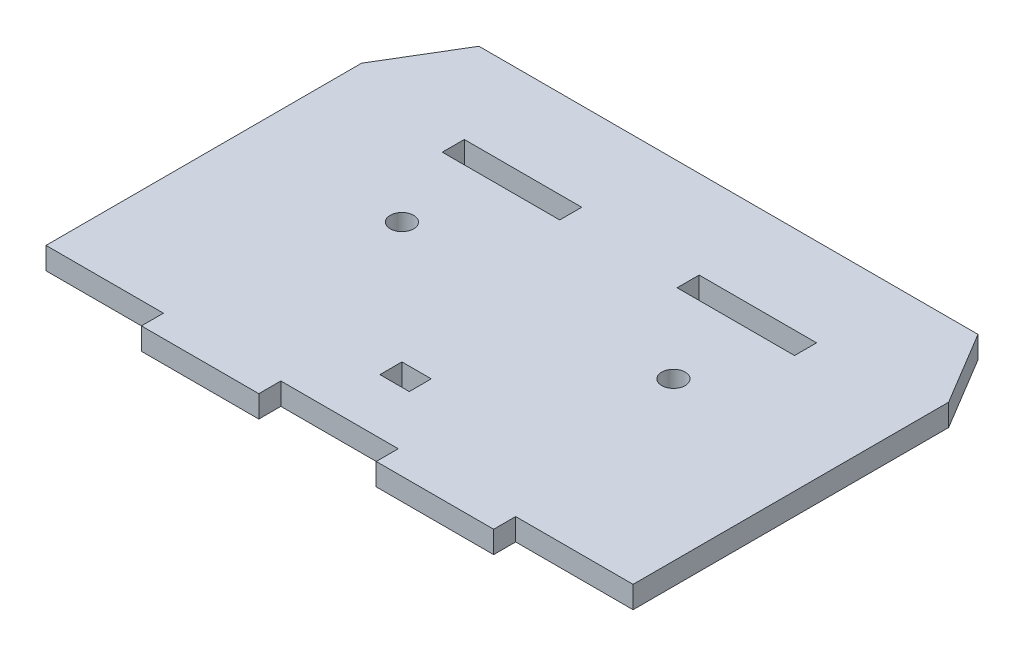
SolidWorks part; units mm, degrees
ref_plane "Ön Düzlem" through (0, 0, 0) normal (0, 0, 1) x (1, 0, 0)
ref_plane "Üst Düzlem" through (0, 0, 0) normal (0, 1, 0) x (1, 0, 0)
ref_plane "Sağ Düzlem" through (0, 0, 0) normal (1, 0, 0) x (0, 0, -1)
sketch "Sketch1" plane through (0, 0, 0) normal (0, 1, 0) x (1, 0, 0)
  line L0 (-40, 37) -> (-34, 47)
  line L1 (-34, 47) -> (34, 47)
  line L2 (-40, 37) -> (-40, -6)
  line L3 (-24, -9) -> (-8, -9)
  line L4 (40, 37) -> (40, -6)
  line L7 (34, 47) -> (40, 37)
  line L9 (-40, -6) -> (-24, -6)
  line L10 (-24, -6) -> (-24, -9)
  line L11 (-8, -9) -> (-8, -6)
  line L12 (-8, -6) -> (8, -6)
  line L13 (8, -6) -> (8, -9)
  line L14 (8, -9) -> (24, -9)
  line L15 (24, -9) -> (24, -6)
  line L16 (24, -6) -> (40, -6)
  point P0 (0, 0)
  dimension "D2" = 43
extrude "Boss-Extrude1" add sketch "Sketch1" along normal blind 3
sketch "Sketch2" plane through (0, 3, 0) normal (0, 1, 0) x (1, 0, 0)
  line L0 (-24, -9) -> (-8, -9) construction
  line L1 (-20, 35) -> (-8, 35) construction
  line L2 (0, 21) -> (0, 3) construction
  line L3 (-20, 35) -> (-24, 35) construction
  line L5 (0, -6) -> (0, 21) construction
  line L6 (-8, -6) -> (8, -6) construction
  line L7 (0, 21) -> (-18.5, 21) construction
  line L8 (0, 21) -> (18.5, 21) construction
  line L9 (-2, 4.5) -> (2, 4.5)
  line L10 (-24, 35) -> (-24, 32)
  line L11 (-24, 32) -> (-8, 32)
  line L12 (-8, 32) -> (-8, 35)
  line L13 (-8, 35) -> (-24, 35)
  line L14 (8, 35) -> (24, 35) construction
  line L15 (8, 32) -> (8, 35)
  line L16 (8, 35) -> (24, 35)
  line L17 (24, 35) -> (24, 32)
  line L18 (24, 32) -> (8, 32)
  line L19 (-2, 4.5) -> (-2, 1.5)
  line L20 (-2, 1.5) -> (2, 1.5)
  line L21 (2, 4.5) -> (2, 1.5)
  line L22 (-2, 4.5) -> (2, 1.5) construction
  line L23 (-2, 1.5) -> (2, 4.5) construction
  circle A0 centre (-18.5, 21) radius 1.6
  circle A1 centre (18.5, 21) radius 1.6
  dimension "D1" = 30
  dimension "D2" = 3
  dimension "D3" = 4
extrude "Cut-Extrude1" cut sketch "Sketch2" against normal through all
